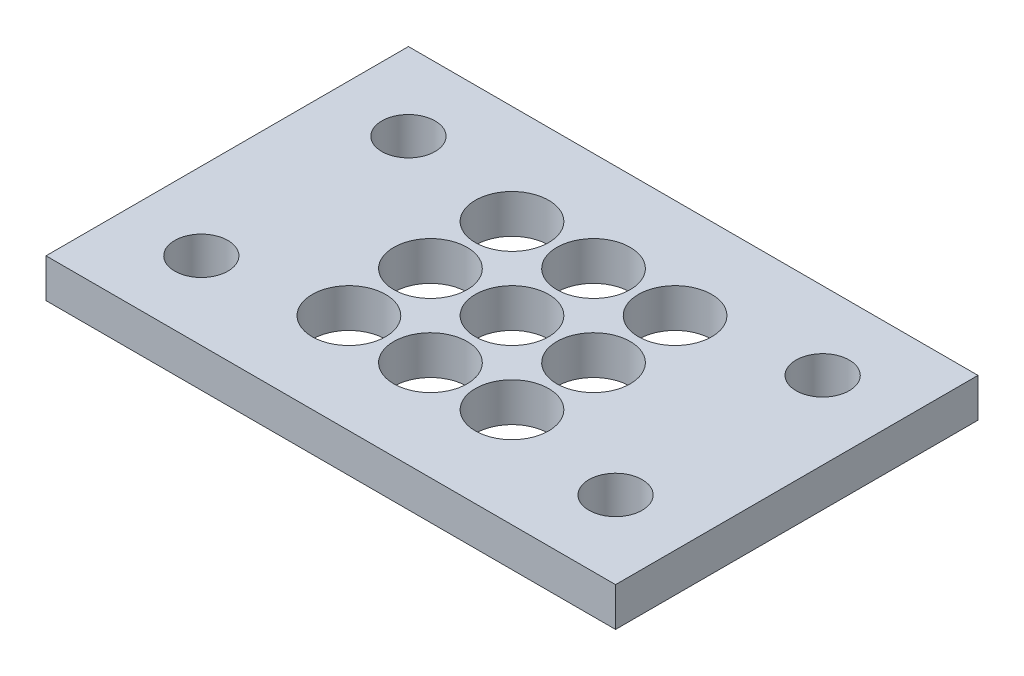
SolidWorks part; units mm, degrees
ref_plane "Front Plane" through (0, 0, 0) normal (0, 0, 1) x (1, 0, 0)
ref_plane "Top Plane" through (0, 0, 0) normal (0, 1, 0) x (1, 0, 0)
ref_plane "Right Plane" through (0, 0, 0) normal (1, 0, 0) x (0, 0, -1)
sketch "Sketch1" plane through (0, 0, 0) normal (0, 1, 0) x (1, 0, 0)
  line L0 (9.525, 34.925) -> (0, 34.925) construction
  line L1 (0, 0) -> (69.85, 0)
  line L2 (0, 0) -> (0, 44.45)
  line L3 (0, 44.45) -> (69.85, 44.45)
  line L4 (69.85, 0) -> (69.85, 44.45)
  line L5 (9.525, 34.925) -> (60.325, 34.925) construction
  line L6 (9.525, 34.925) -> (9.525, 9.525) construction
  line L7 (9.525, 9.525) -> (60.325, 9.525) construction
  line L8 (60.325, 34.925) -> (60.325, 9.525) construction
  line L9 (9.525, 34.925) -> (9.525, 44.45) construction
  circle A0 centre (9.525, 34.925) radius 3.2639
  circle A1 centre (60.325, 34.925) radius 3.2639
  circle A2 centre (9.525, 9.525) radius 3.2639
  circle A3 centre (60.325, 9.525) radius 3.2639
  circle A4 centre (34.925, 22.225) radius 4.5
  circle A5 centre (44.925, 22.225) radius 4.5
  circle A6 centre (44.925, 32.225) radius 4.5
  circle A7 centre (34.925, 32.225) radius 4.5
  circle A8 centre (24.925, 22.225) radius 4.5
  circle A9 centre (24.925, 32.225) radius 4.5
  circle A10 centre (34.925, 32.225) radius 4.5
  circle A11 centre (24.925, 22.225) radius 4.5
  circle A12 centre (24.925, 12.225) radius 4.5
  circle A13 centre (34.925, 12.225) radius 4.5
  circle A14 centre (44.925, 22.225) radius 4.5
  circle A15 centre (44.925, 12.225) radius 4.5
  circle A16 centre (34.925, 12.225) radius 4.5
  point P13 (34.925, 34.925)
  point P14 (34.925, 44.45)
  point P20 (69.85, 22.225)
  dimension "D5" = 6.5278
  dimension "D6" = 9
  dimension "D1" = 69.85
  dimension "D2" = 44.45
  dimension "D3" = 50.8
  dimension "D4" = 25.4
  dimension "D15" = 10
  dimension "D16" = 10
  dimension "D17" = 10
  dimension "D18" = 10
  dimension "D19" = 10
  dimension "D20" = 10
  dimension "D21" = 10
  dimension "D22" = 10
  dimension "D7" = 2
  dimension "D8" = 2
  dimension "D9" = 2
  dimension "D10" = 2
  dimension "D11" = 2
  dimension "D12" = 2
  dimension "D13" = 2
  dimension "D14" = 2
extrude "Boss-Extrude1" add sketch "Sketch1" along normal blind 4.7625 contours L1 L4 L3 L2 A15 A13 A12 A9 A8 A7 A6 A5 A4 A3 A2 A1 A0
